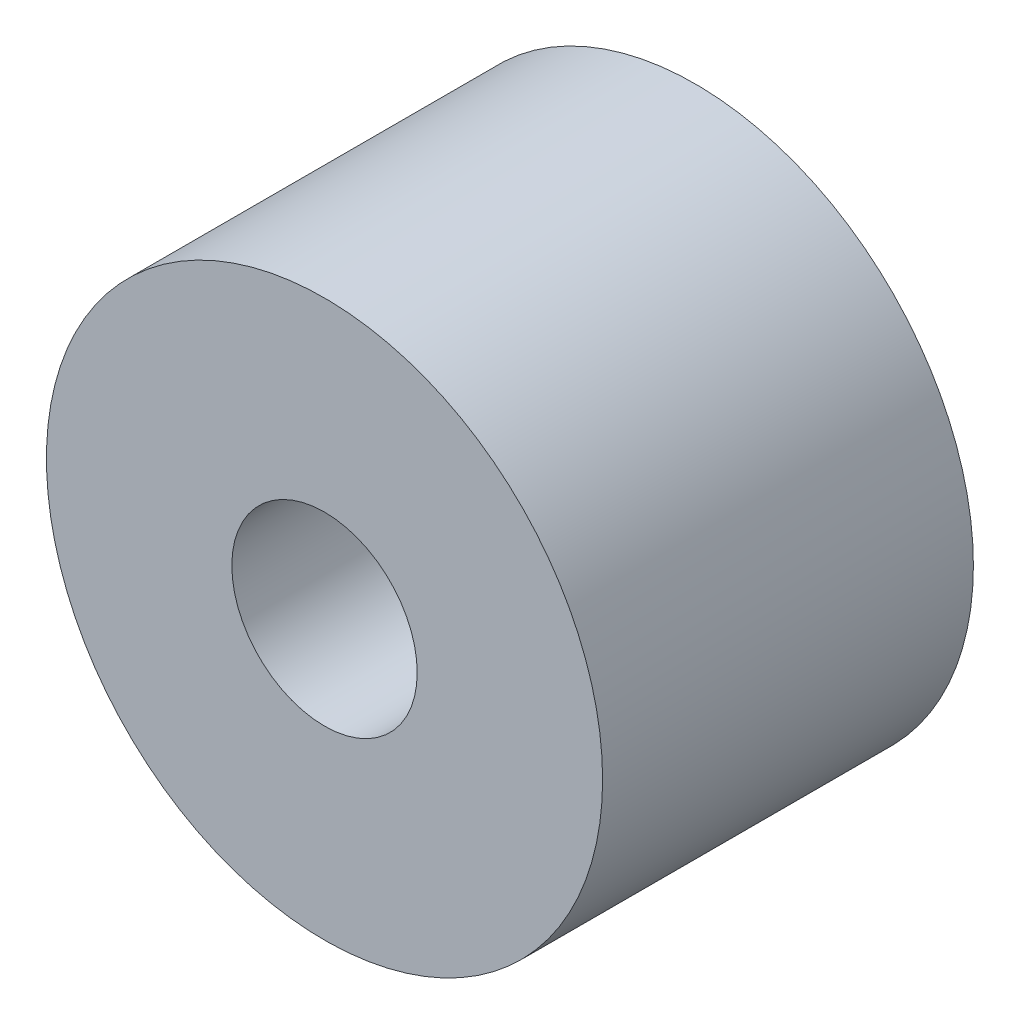
SolidWorks part; units mm, degrees
ref_plane "Front Plane" through (0, 0, 0) normal (0, 0, 1) x (1, 0, 0)
ref_plane "Top Plane" through (0, 0, 0) normal (0, 1, 0) x (1, 0, 0)
ref_plane "Right Plane" through (0, 0, 0) normal (1, 0, 0) x (0, 0, -1)
sketch "Sketch1" plane through (0, 0, 0) normal (0, 0, 1) x (1, 0, 0)
  circle A0 centre (0, 0) radius 15
  dimension "D1" = 30
extrude "Boss-Extrude1" add sketch "Sketch1" along normal blind 20
sketch "Sketch2" plane through (0, 0, 20) normal (0, 0, 1) x (1, 0, 0)
  circle A0 centre (0, 0) radius 5
  dimension "D1" = 10
extrude "Cut-Extrude1" cut sketch "Sketch2" against normal blind 10
